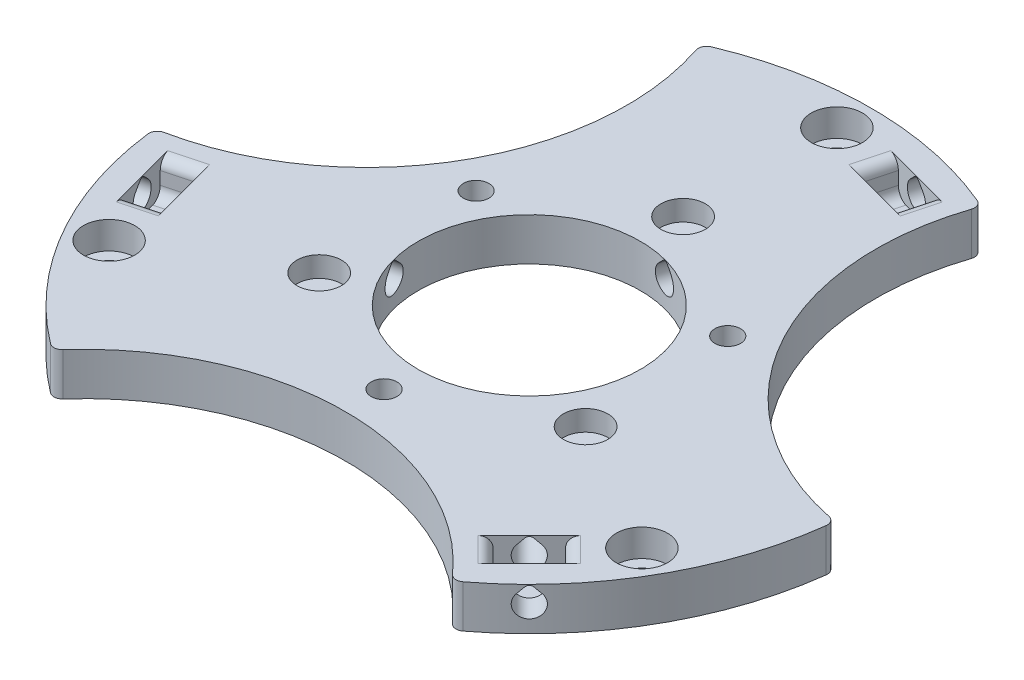
SolidWorks part; units mm, degrees
ref_plane "Front Plane" through (0, 0, 0) normal (0, 0, 1) x (1, 0, 0)
ref_plane "Top Plane" through (0, 0, 0) normal (0, 1, 0) x (1, 0, 0)
ref_plane "Right Plane" through (0, 0, 0) normal (1, 0, 0) x (0, 0, -1)
sketch "Sketch1" plane through (0, 0, 0) normal (0, 1, 0) x (1, 0, 0)
  circle A0 centre (0, 0) radius 40
  circle A1 centre (0, 0) radius 13
  dimension "D1" = 80
  dimension "D2" = 26
extrude "Boss-Extrude1" add sketch "Sketch1" along normal blind 5
sketch "Sketch2" plane through (0, 5, 0) normal (0, 1, 0) x (1, 0, 0)
  circle A0 centre (0, 36) radius 1.65
  dimension "D1" = 3.3
  dimension "D2" = 36
extrude "Cut-Extrude1" cut sketch "Sketch2" against normal through all
pattern_circular "CirPattern1" count 3 over 360 about axis through (0, 0, 0) along (0, 1, 0) of "Cut-Extrude1"
sketch "Sketch3" plane through (0, 5, 0) normal (0, 1, 0) x (1, 0, 0)
  line L0 (0, 0) -> (45.0333, 26) construction
  line L1 (-1000, 0) -> (49000, 0) construction
  circle A0 centre (45.0333, 26) radius 30.47
  dimension "D2" = 60.94
  dimension "D1" = 30
  dimension "D3" = 52
extrude "Cut-Extrude2" cut sketch "Sketch3" against normal blind 10
pattern_circular "CirPattern2" count 3 over 360 about axis through (0, 0, 0) along (0, 1, 0) of "Cut-Extrude2"
fillet "Fillet1" radius 1 6 edges at (23.3776, 2.5, 32.4575) (-23.3776, 2.5, 32.4575) (-39.7978, 2.5, 4.0168) (-16.4202, 2.5, -36.4743) (16.4202, 2.5, -36.4743) (39.7978, 2.5, 4.0168)
sketch "Sketch4" plane through (0, 5, 0) normal (0, 1, 0) x (1, 0, 0)
  circle A0 centre (0, 0) radius 6 construction
  circle A1 centre (0, 18) radius 12 construction
  circle A2 centre (0, 18) radius 0.75
  dimension "D1" = 12
  dimension "D2" = 24
  dimension "D3" = 1.5
extrude "Cut-Extrude3" cut sketch "Sketch4" against normal blind 10
sketch "Sketch6" plane through (0, 5, 0) normal (0, 1, 0) x (1, 0, 0)
  circle A0 centre (0, 18) radius 2.6
  dimension "D1" = 5.2
extrude "Cut-Extrude4" cut sketch "Sketch6" against normal blind 2.4
sketch "Sketch7" plane through (0, 5, 0) normal (0, 1, 0) x (1, 0, 0)
  circle A0 centre (0, 36) radius 3
  dimension "D1" = 6
extrude "Cut-Extrude5" cut sketch "Sketch7" against normal blind 3.2
pattern_circular "CirPattern3" count 3 over 360 about axis through (0, 0, 0) along (0, 1, 0) of "Cut-Extrude3", "Cut-Extrude4", "Cut-Extrude5"
sketch "Sketch8" plane through (0, 5, 0) normal (0, 1, 0) x (1, 0, 0)
  line L0 (14.7224, 8.5) -> (0, 0) construction
  line L1 (-1000, 0) -> (49000, 0) construction
  circle A0 centre (14.7224, 8.5) radius 1.5
  dimension "D3" = 3
  dimension "D1" = 30
  dimension "D2" = 17
extrude "Cut-Extrude6" cut sketch "Sketch8" against normal blind 10
pattern_circular "CirPattern4" count 3 over 360 about axis through (0, 0, 0) along (0, 1, 0) of "Cut-Extrude6"
sketch "Sketch9" plane through (0, 5, 0) normal (0, 1, 0) x (1, 0, 0)
  line L0 (0, 0) -> (11.4379, 42.6867) construction
  line L1 (5.6433, 32.652) -> (11.4388, 31.0991)
  line L2 (5.6433, 32.652) -> (6.6785, 36.5157)
  line L3 (11.4388, 31.0991) -> (12.4741, 34.9628)
  line L4 (6.6785, 36.5157) -> (12.4741, 34.9628)
  line L5 (5.6433, 32.652) -> (12.4741, 34.9628) construction
  line L6 (11.4388, 31.0991) -> (6.6785, 36.5157) construction
  line L7 (0, -1000) -> (0, 49000) construction
  point P4 (9.0587, 33.8074)
  dimension "D1" = 15
  dimension "D2" = 4
  dimension "D3" = 6
  dimension "D4" = 35
extrude "Cut-Extrude7" cut sketch "Sketch9" against normal blind 4
sketch "Sketch10" plane through (8.541, 0, -31.8756) normal (0.2588, 0, -0.9659) x (-0.9659, 0, -0.2588)
  line L0 (-997.1174, 5.5) -> (49002.8826, 5.5) construction
  line L1 (24.5667, 5) -> (-5.4919, 5) construction
  line L6 (-0.3767, 4.7446) -> (-1.0607, 4.0607)
  line L7 (0.3767, 4.7446) -> (1.0607, 4.0607)
  circle A0 centre (0, 3) radius 2.5 construction
  arc A1 (-1.0607, 4.0607) -> (1.0607, 4.0607) centre (0, 3) ccw
  arc A2 (0.3767, 4.7446) -> (-0.3767, 4.7446) centre (0, 4.3679) ccw
  dimension "D1" = 5
  dimension "D3" = 3
  dimension "D2" = 0.5
extrude "Cut-Extrude8" cut sketch "Sketch10" against normal blind 25 and the other way through all
fillet "Fillet3" radius 1.25 4 edges at (6.1609, 5, -34.5839) (6.1609, 1, -34.5839) (11.9564, 5, -33.0309) (11.9564, 1, -33.0309)
pattern_circular "CirPattern5" count 3 over 360 about axis through (0, 0, 0) along (0, 1, 0) of "Cut-Extrude7", "Cut-Extrude8", "Fillet3"
